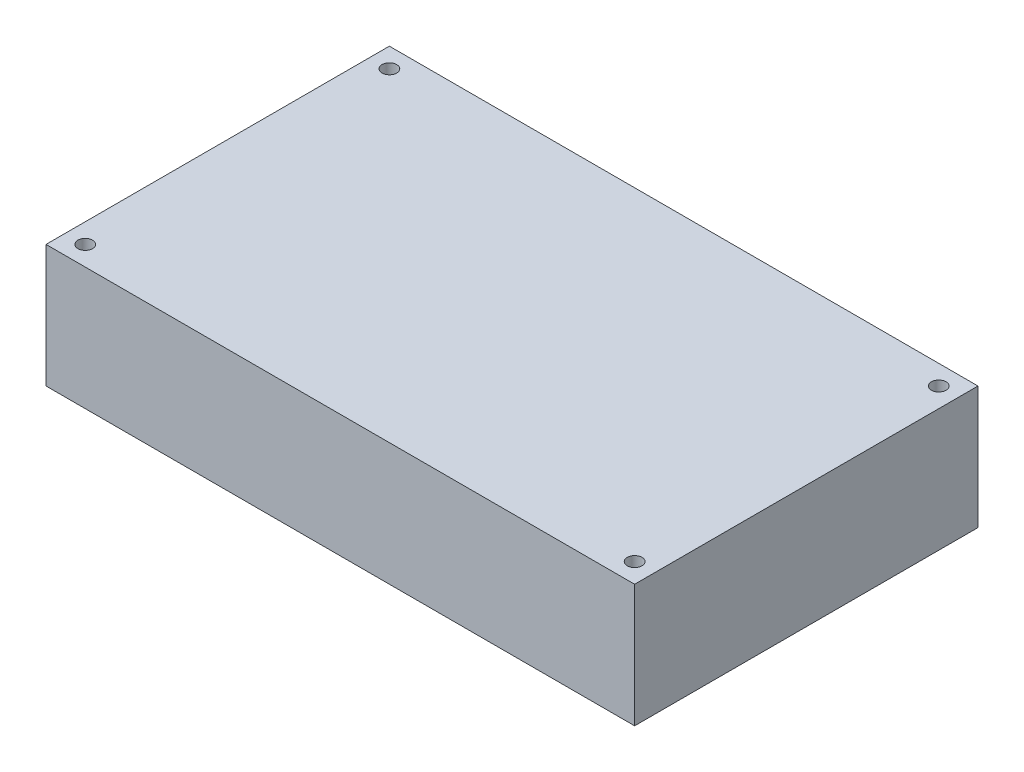
SolidWorks part; units mm, degrees
ref_plane "Front Plane" through (0, 0, 0) normal (0, 0, 1) x (1, 0, 0)
ref_plane "Top Plane" through (0, 0, 0) normal (0, 1, 0) x (1, 0, 0)
ref_plane "Right Plane" through (0, 0, 0) normal (1, 0, 0) x (0, 0, -1)
sketch "Sketch1" plane through (0, 0, 0) normal (0, 1, 0) x (1, 0, 0)
  line L1 (-60, 35) -> (60, 35)
  line L2 (-60, 35) -> (-60, -35)
  line L3 (-60, -35) -> (60, -35)
  line L4 (60, 35) -> (60, -35)
  line L5 (-60, 35) -> (60, -35) construction
  line L6 (-60, -35) -> (60, 35) construction
  point P0 (0, 0)
  dimension "D1" = 70
  dimension "D2" = 120
extrude "Boss-Extrude1" add sketch "Sketch1" along normal blind 25
sketch "Sketch2" plane through (0, 25, 0) normal (0, 1, 0) x (1, 0, 0)
  line L1 (-56, 31) -> (56, 31) construction
  line L2 (-56, 31) -> (-56, -31) construction
  line L3 (-56, -31) -> (56, -31) construction
  line L4 (56, 31) -> (56, -31) construction
  line L5 (-56, 31) -> (56, -31) construction
  line L6 (-56, -31) -> (56, 31) construction
  circle A0 centre (-56, 31) radius 1.5
  circle A1 centre (56, 31) radius 1.5
  circle A2 centre (56, -31) radius 1.5
  circle A3 centre (-56, -31) radius 1.5
  point P0 (0, 0)
  dimension "D3" = 3
  dimension "D1" = 112
  dimension "D2" = 62
extrude "Cut-Extrude1" cut sketch "Sketch2" against normal through all both and the other way through all
